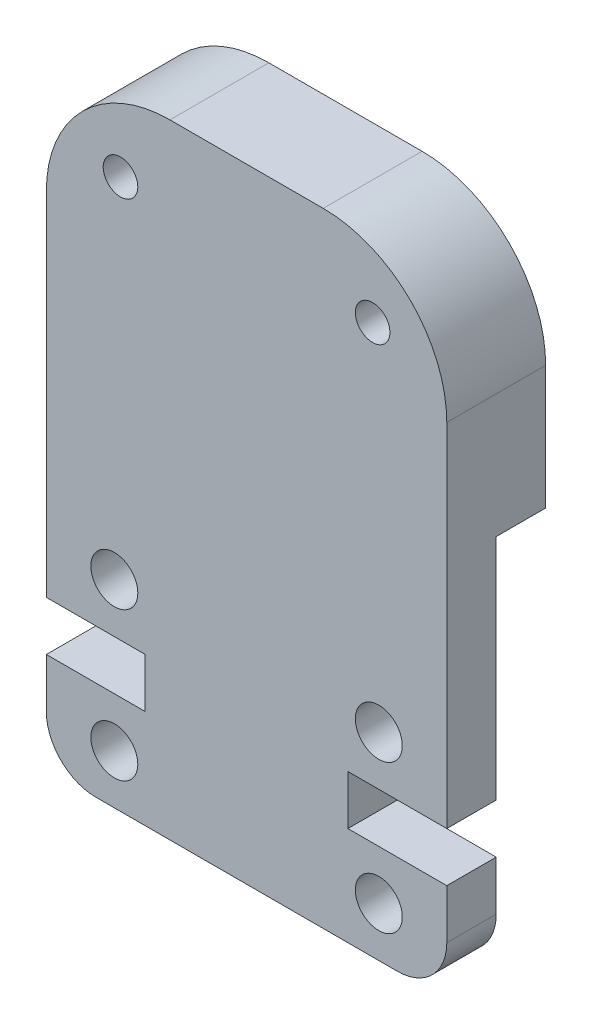
SolidWorks part; units mm, degrees
ref_plane "Front Plane" through (0, 0, 0) normal (0, 0, 1) x (1, 0, 0)
ref_plane "Top Plane" through (0, 0, 0) normal (0, 1, 0) x (1, 0, 0)
ref_plane "Right Plane" through (0, 0, 0) normal (1, 0, 0) x (0, 0, -1)
sketch "Sketch1" plane through (0, 0, 0) normal (0, 0, 1) x (1, 0, 0)
  line L0 (8.1, 25.23) -> (8.1, 0) construction
  line L1 (2, 0) -> (14.2, 0)
  line L2 (5, 25.23) -> (11.2, 25.23)
  line L3 (12.2, 4) -> (16.2, 4)
  line L4 (12.2, 6) -> (12.2, 4)
  line L5 (16.2, 6) -> (12.2, 6)
  line L6 (16.2, 2) -> (16.2, 4)
  line L7 (16.2, 20.23) -> (16.2, 6)
  line L22 (0, 20.23) -> (0, 6)
  line L33 (0, 2) -> (0, 4)
  line L34 (0, 6) -> (4, 6)
  line L36 (4, 6) -> (4, 4)
  line L37 (4, 4) -> (0, 4)
  circle A0 centre (13.45, 2) radius 0.95
  arc A1 (16.2, 2) -> (14.2, 0) centre (14.2, 2) cw
  circle A2 centre (13.2, 22.23) radius 0.7
  arc A3 (11.2, 25.23) -> (16.2, 20.23) centre (11.2, 20.23) cw
  circle A4 centre (2.75, 8) radius 0.95
  circle A5 centre (13.45, 8) radius 0.95
  arc A17 (5, 25.23) -> (0, 20.23) centre (5, 20.23) ccw
  circle A19 centre (3, 22.23) radius 0.7
  arc A21 (0, 2) -> (2, 0) centre (2, 2) ccw
  circle A23 centre (2.75, 2) radius 0.95
  dimension "D1" = 1.4
  dimension "D2" = 6
  dimension "D3" = 5
  dimension "D4" = 2
  dimension "D14" = 1.9
  dimension "D10" = 1.9
  dimension "D11" = 1.9
  dimension "D15" = 1.9
  dimension "D5" = 3
  dimension "D6" = 2.75
  dimension "D7" = 8.1
  dimension "D8" = 2.75
  dimension "D9" = 4
  dimension "D12" = 3
  dimension "D13" = 25.23
extrude "Boss-Extrude1" add sketch "Sketch1" along normal blind 4
sketch "Sketch2" plane through (0, 0, 0) normal (0, 0, 1) x (1, 0, 0)
  line L0 (0, 0) -> (16.2, 0)
  line L1 (16.2, 0) -> (16.2, 15.23)
  line L2 (16.2, 15.23) -> (0, 15.23)
  line L3 (0, 15.23) -> (0, 0)
  dimension "D1" = 15.23
extrude "Cut-Extrude1" cut sketch "Sketch2" along normal blind 2
equation "\"D7@Sketch1\"= \"fingerWidth@parametersSketch@prostheticParameters.SLDPRT\" / 2 'DIP width"
equation "\"D13@Sketch1\"= \"HL@parametersSketch@prostheticParameters.SLDPRT\" * 0.158 - 4 'DIP length - Sil. Sht DIP"
equation "\"D1@Sketch2\"= \"HL@parametersSketch@prostheticParameters.SLDPRT\" * 0.158 - 4 - 10 'DIP Cut fingertip"
equation "\"D1@Sketch1\"= 1 + \"tol1@parametersSketch@prostheticParameters.SLDPRT\""
equation "\"D10@Sketch1\"= 1.5 + \"tol1@parametersSketch@prostheticParameters.SLDPRT\""
equation "\"D11@Sketch1\"= 1.5 + \"tol1@parametersSketch@prostheticParameters.SLDPRT\""
equation "\"D14@Sketch1\"= 1.5 + \"tol1@parametersSketch@prostheticParameters.SLDPRT\""
equation "\"D15@Sketch1\"= 1.5 + \"tol1@parametersSketch@prostheticParameters.SLDPRT\""
